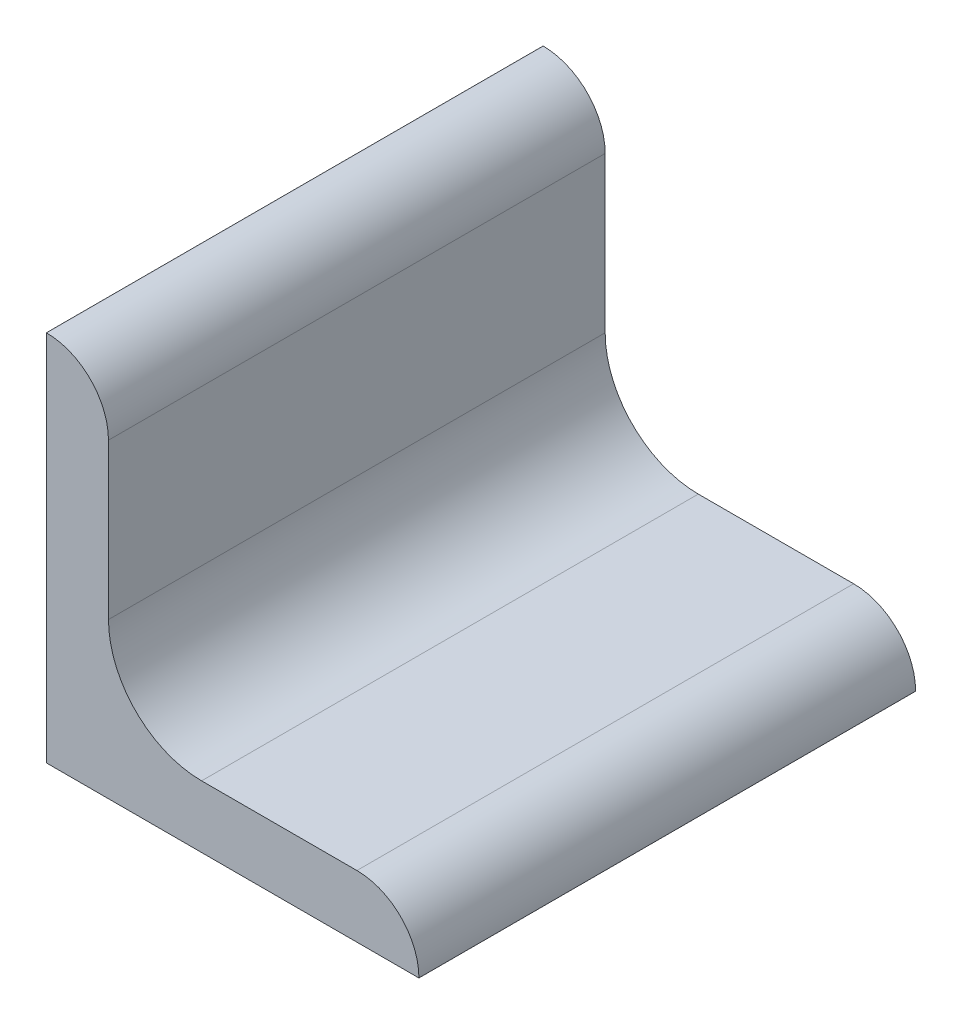
SolidWorks part; units mm, degrees
ref_plane "Plane1" through (0, 0, 0) normal (0, 0, 1) x (1, 0, 0)
ref_plane "Plane2" through (0, 0, 0) normal (0, 1, 0) x (1, 0, 0)
ref_plane "Plane3" through (0, 0, 0) normal (1, 0, 0) x (0, 0, -1)
sketch "Sketch1" plane through (0, 0, 0) normal (0, 0, 1) x (1, 0, 0)
  line L0 (0, 0) -> (0, 19.05)
  line L1 (0, 19.05) -> (0.0051, 19.05)
  line L2 (3.175, 15.8801) -> (3.175, 7.9375)
  line L3 (7.9375, 3.175) -> (15.8801, 3.175)
  line L4 (19.05, 0.0051) -> (19.05, 0)
  line L5 (19.05, 0) -> (0, 0)
  arc A0 (19.05, 0.0051) -> (15.8801, 3.175) centre (15.8801, 0.0051) ccw
  arc A1 (0.0051, 19.05) -> (3.175, 15.8801) centre (0.0051, 15.8801) cw
  arc A2 (7.9375, 3.175) -> (3.175, 7.9375) centre (7.9375, 7.9375) cw
  circle A3 centre (0, 0) radius 3.175 construction
  dimension "D2" = 0.0051
  dimension "Radius_1" = 4.7625
  dimension "Radius_2" = 3.175
  dimension "D1" = 3.175
  dimension "V_leg" = 19.05
  dimension "H_leg" = 19.05
  dimension "Thickness" = 3.175
  dimension "Flat_wid" = 0.0051
extrude "BaseSteelAngle" add sketch "Sketch1" along normal mid plane 25.4
equation "\"Flat_wid@Sketch1\" = ((sgn(\"Thickness@Sketch1\" - \"Radius_2@Sketch1\") +1)*(\"Thickness@Sketch1\" - \"Radius_2@Sketch1\"))/2 +0.0002"
equation "\"D1@Sketch1\" = \"Thickness@Sketch1\""
equation "\"D2@Sketch1\" = \"Flat_wid@Sketch1\""
